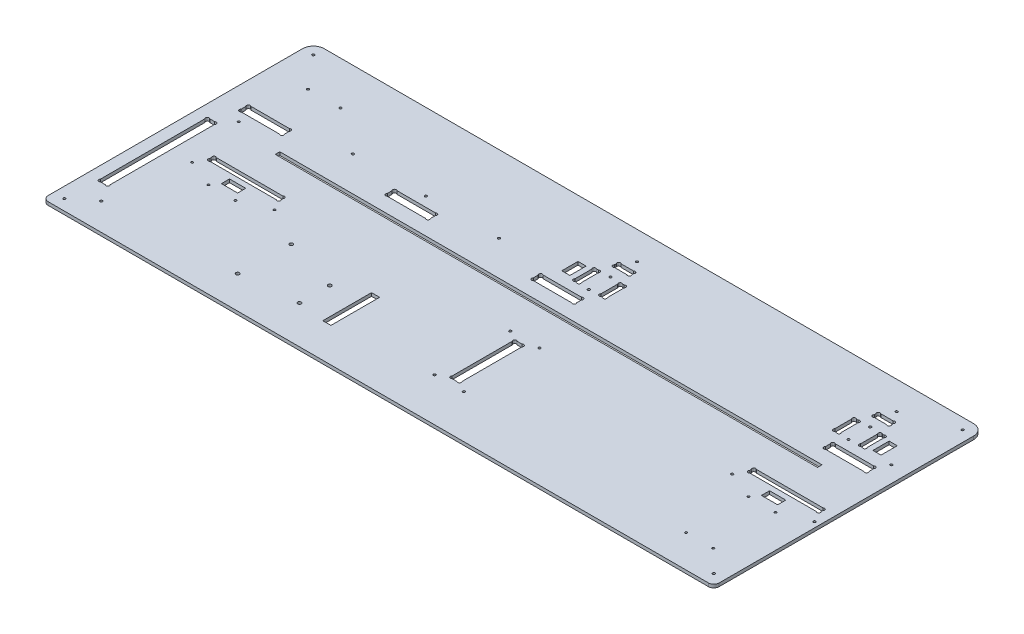
SolidWorks part; units mm, degrees
ref_plane "Plan de face" through (0, 0, 0) normal (0, 0, 1) x (1, 0, 0)
ref_plane "Plan de dessus" through (0, 0, 0) normal (0, 1, 0) x (1, 0, 0)
ref_plane "Plan de droite" through (0, 0, 0) normal (1, 0, 0) x (0, 0, -1)
sketch "Esquisse1" plane through (0, 0, 0) normal (0, 1, 0) x (1, 0, 0)
  line L26 (317, 211.2627) -> (317, 212.7373)
  line L28 (319.2627, 215) -> (330.7373, 215)
  line L29 (333, 211.2627) -> (333, 212.7373)
  line L30 (330.7373, 209) -> (319.2627, 209)
  line L31 (312.2627, 179.5) -> (313.7373, 179.5)
  line L32 (312.2627, 199.5) -> (313.7373, 199.5)
  line L33 (310, 197.2373) -> (310, 181.7627)
  line L34 (316, 181.7627) -> (316, 197.2373)
  line L35 (334, 181.7627) -> (334, 197.2373)
  line L36 (340, 197.2373) -> (340, 181.7627)
  line L37 (337.7373, 199.5) -> (336.2627, 199.5)
  line L38 (337.7373, 179.5) -> (336.2627, 179.5)
  line L39 (552.2627, 179.5) -> (553.7373, 179.5)
  line L40 (552.2627, 199.5) -> (553.7373, 199.5)
  line L41 (550, 197.2373) -> (550, 181.7627)
  line L42 (556, 181.7627) -> (556, 197.2373)
  line L43 (574, 181.7627) -> (574, 197.2373)
  line L44 (580, 197.2373) -> (580, 181.7627)
  line L45 (577.7373, 199.5) -> (576.2627, 199.5)
  line L46 (577.7373, 179.5) -> (576.2627, 179.5)
  line L47 (559.2627, 209) -> (570.7373, 209)
  line L48 (557, 211.2627) -> (557, 212.7373)
  line L49 (570.7373, 215) -> (559.2627, 215)
  line L50 (573, 211.2627) -> (573, 212.7373)
  line L55 (560, 167.7373) -> (560, 163.2627)
  line L56 (600, 167.7373) -> (600, 163.2627)
  line L57 (562.2627, 170) -> (597.7373, 170)
  line L58 (597.7373, 161) -> (562.2627, 161)
  line L59 (292.2627, 161) -> (327.7373, 161)
  line L60 (327.7373, 170) -> (292.2627, 170)
  line L61 (290, 167.7373) -> (290, 163.2627)
  line L62 (330, 167.7373) -> (330, 163.2627)
  line L64 (20, 167.7373) -> (20, 163.2627)
  line L65 (60, 167.7373) -> (60, 163.2627)
  line L66 (22.2627, 170) -> (57.7373, 170)
  line L67 (57.7373, 161) -> (22.2627, 161)
  line L70 (155, 167.7373) -> (155, 163.2627)
  line L71 (195, 167.7373) -> (195, 163.2627)
  line L72 (157.2627, 170) -> (192.7373, 170)
  line L73 (192.7373, 161) -> (157.2627, 161)
  line L76 (10, 250) -> (610, 250)
  line L77 (0, 240) -> (0, 0)
  line L78 (0, 0) -> (620, 0)
  line L79 (620, 240) -> (620, 0)
  line L84 (13.2627, 40) -> (17.7373, 40)
  line L85 (13.2627, 141) -> (17.7373, 141)
  line L86 (11, 138.7373) -> (11, 42.2627)
  line L87 (20, 42.2627) -> (20, 138.7373)
  line L98 (337.7373, 45) -> (333.2627, 45)
  line L99 (337.7373, 105) -> (333.2627, 105)
  line L100 (340, 47.2627) -> (340, 102.7373)
  line L101 (331, 102.7373) -> (331, 47.2627)
  line L109 (610, 109.2627) -> (610, 110.7373)
  line L110 (544, 109.2627) -> (544, 110.7373)
  line L111 (607.7373, 107) -> (546.2627, 107)
  line L112 (546.2627, 113) -> (607.7373, 113)
  line L113 (108.7373, 113) -> (47.2627, 113)
  line L114 (47.2627, 107) -> (108.7373, 107)
  line L115 (111, 109.2627) -> (111, 110.7373)
  line L116 (45, 109.2627) -> (45, 110.7373)
  arc A0 (319.2627, 215) -> (317, 212.7373) centre (318.1314, 213.8686) ccw
  arc A1 (319.2627, 209) -> (317, 211.2627) centre (318.1314, 210.1314) cw
  arc A2 (330.7373, 209) -> (333, 211.2627) centre (331.8686, 210.1314) ccw
  arc A3 (330.7373, 215) -> (333, 212.7373) centre (331.8686, 213.8686) cw
  arc A4 (313.7373, 179.5) -> (316, 181.7627) centre (314.8686, 180.6314) ccw
  arc A5 (312.2627, 179.5) -> (310, 181.7627) centre (311.1314, 180.6314) cw
  arc A6 (312.2627, 199.5) -> (310, 197.2373) centre (311.1314, 198.3686) ccw
  arc A7 (313.7373, 199.5) -> (316, 197.2373) centre (314.8686, 198.3686) cw
  arc A8 (336.2627, 179.5) -> (334, 181.7627) centre (335.1314, 180.6314) cw
  arc A9 (336.2627, 199.5) -> (334, 197.2373) centre (335.1314, 198.3686) ccw
  arc A10 (337.7373, 199.5) -> (340, 197.2373) centre (338.8686, 198.3686) cw
  arc A11 (337.7373, 179.5) -> (340, 181.7627) centre (338.8686, 180.6314) ccw
  arc A12 (552.2627, 179.5) -> (550, 181.7627) centre (551.1314, 180.6314) cw
  arc A13 (552.2627, 199.5) -> (550, 197.2373) centre (551.1314, 198.3686) ccw
  arc A14 (553.7373, 199.5) -> (556, 197.2373) centre (554.8686, 198.3686) cw
  arc A15 (553.7373, 179.5) -> (556, 181.7627) centre (554.8686, 180.6314) ccw
  arc A16 (576.2627, 199.5) -> (574, 197.2373) centre (575.1314, 198.3686) ccw
  arc A17 (577.7373, 199.5) -> (580, 197.2373) centre (578.8686, 198.3686) cw
  arc A18 (577.7373, 179.5) -> (580, 181.7627) centre (578.8686, 180.6314) ccw
  arc A19 (576.2627, 179.5) -> (574, 181.7627) centre (575.1314, 180.6314) cw
  arc A20 (559.2627, 215) -> (557, 212.7373) centre (558.1314, 213.8686) ccw
  arc A21 (559.2627, 209) -> (557, 211.2627) centre (558.1314, 210.1314) cw
  arc A22 (570.7373, 209) -> (573, 211.2627) centre (571.8686, 210.1314) ccw
  arc A23 (570.7373, 215) -> (573, 212.7373) centre (571.8686, 213.8686) cw
  arc A29 (560, 163.2627) -> (562.2627, 161) centre (561.1314, 162.1314) ccw
  arc A30 (560, 167.7373) -> (562.2627, 170) centre (561.1314, 168.8686) cw
  arc A31 (600, 167.7373) -> (597.7373, 170) centre (598.8686, 168.8686) ccw
  arc A32 (600, 163.2627) -> (597.7373, 161) centre (598.8686, 162.1314) cw
  arc A34 (290, 163.2627) -> (292.2627, 161) centre (291.1314, 162.1314) ccw
  arc A35 (290, 167.7373) -> (292.2627, 170) centre (291.1314, 168.8686) cw
  arc A36 (330, 167.7373) -> (327.7373, 170) centre (328.8686, 168.8686) ccw
  arc A37 (330, 163.2627) -> (327.7373, 161) centre (328.8686, 162.1314) cw
  arc A40 (20, 163.2627) -> (22.2627, 161) centre (21.1314, 162.1314) ccw
  arc A41 (20, 167.7373) -> (22.2627, 170) centre (21.1314, 168.8686) cw
  arc A42 (60, 167.7373) -> (57.7373, 170) centre (58.8686, 168.8686) ccw
  arc A43 (60, 163.2627) -> (57.7373, 161) centre (58.8686, 162.1314) cw
  arc A44 (155, 163.2627) -> (157.2627, 161) centre (156.1314, 162.1314) ccw
  arc A45 (155, 167.7373) -> (157.2627, 170) centre (156.1314, 168.8686) cw
  arc A46 (195, 163.2627) -> (192.7373, 161) centre (193.8686, 162.1314) cw
  arc A47 (195, 167.7373) -> (192.7373, 170) centre (193.8686, 168.8686) ccw
  arc A50 (17.7373, 40) -> (20, 42.2627) centre (18.8686, 41.1314) ccw
  arc A52 (13.2627, 40) -> (11, 42.2627) centre (12.1314, 41.1314) cw
  arc A53 (17.7373, 141) -> (20, 138.7373) centre (18.8686, 139.8686) cw
  arc A54 (13.2627, 141) -> (11, 138.7373) centre (12.1314, 139.8686) ccw
  arc A56 (10, 250) -> (0, 240) centre (10, 240) ccw
  arc A57 (610, 250) -> (620, 240) centre (610, 240) cw
  arc A59 (331, 47.2627) -> (333.2627, 45) centre (332.1314, 46.1314) ccw
  arc A60 (340, 47.2627) -> (337.7373, 45) centre (338.8686, 46.1314) cw
  arc A61 (331, 102.7373) -> (333.2627, 105) centre (332.1314, 103.8686) cw
  arc A62 (340, 102.7373) -> (337.7373, 105) centre (338.8686, 103.8686) ccw
  arc A64 (607.7373, 107) -> (610, 109.2627) centre (608.8686, 108.1314) ccw
  circle A65 centre (539, 98) radius 1.1
  arc A66 (607.7373, 113) -> (610, 110.7373) centre (608.8686, 111.8686) cw
  circle A67 centre (615, 98) radius 1.1
  arc A68 (546.2627, 113) -> (544, 110.7373) centre (545.1314, 111.8686) ccw
  arc A69 (546.2627, 107) -> (544, 109.2627) centre (545.1314, 108.1314) cw
  arc A70 (108.7373, 107) -> (111, 109.2627) centre (109.8686, 108.1314) ccw
  arc A71 (108.7373, 113) -> (111, 110.7373) centre (109.8686, 111.8686) cw
  arc A73 (47.2627, 113) -> (45, 110.7373) centre (46.1314, 111.8686) ccw
  arc A75 (47.2627, 107) -> (45, 109.2627) centre (46.1314, 108.1314) cw
  point P1 (337, 199.5)
  point P7 (340, 189.5)
  dimension "D25" = 6
  dimension "D28" = 16
  dimension "D29" = 20
  dimension "D32" = 9.5
  dimension "D33" = 35
  dimension "D39" = 10
  dimension "D49" = 1.1314
  dimension "D57" = 6
  dimension "D55" = 10
  dimension "D62" = 5
  dimension "D63" = 1.6
  dimension "D64" = 9
  dimension "D65" = 1.1314
  dimension "D66" = 1.1314
  dimension "D67" = 620
  dimension "D9" = 2.2627
  dimension "D10" = 1.6
  dimension "D78" = 3.7373
  dimension "D14" = 1.6
  dimension "D36" = 1.6
  dimension "D61" = 1.6
  dimension "D95" = 1.6
  dimension "D107" = 1.6
  dimension "D118" = 1.6
  dimension "D119" = 1.6
  dimension "D128" = 6
  dimension "D141" = 1.6
  dimension "D58" = 2.2
  dimension "D2" = 250
  dimension "D8" = 20
  dimension "D13" = 40
  dimension "D16" = 1.1314
  dimension "D17" = 1.1314
  dimension "D19" = 2.2627
  dimension "D20" = 2.2627
  dimension "D21" = 80
  dimension "D22" = 9
  dimension "D23" = 1.1314
  dimension "D24" = 1.1314
  dimension "D26" = 6
  dimension "D27" = 6
  dimension "D30" = 40
  dimension "D31" = 18
  dimension "D37" = 1.1314
  dimension "D38" = 2.2627
  dimension "D40" = 1.1314
  dimension "D41" = 1.1314
  dimension "D42" = 1.1314
  dimension "D43" = 1.1314
  dimension "D45" = 1
  dimension "D46" = 1.1314
  dimension "D47" = 1.1314
  dimension "D48" = 1.1314
  dimension "D51" = 3.7373
  dimension "D52" = 66
  dimension "D53" = 10
  dimension "D54" = 66
  dimension "D56" = 107
  dimension "D59" = 1.1314
  dimension "D60" = 2.2627
  dimension "D68" = 60
  dimension "D70" = 6
  dimension "D72" = 1.1314
  dimension "D73" = 1.1314
  dimension "D74" = 63.7373
  dimension "D75" = 2.2627
  dimension "D76" = 2.2627
  dimension "D77" = 45
  dimension "D79" = 45
  dimension "D83" = 280
  dimension "D84" = 1.1314
  dimension "D85" = 1.1314
  dimension "D86" = 1.1314
  dimension "D87" = 1.1314
  dimension "D88" = 9
  dimension "D89" = 101
  dimension "D90" = 40
  dimension "D91" = 11
  dimension "D96" = 1.1314
  dimension "D97" = 1.1314
  dimension "D98" = 1.1314
  dimension "D100" = 1.1314
  dimension "D105" = 9
  dimension "D106" = 40
  dimension "D108" = 20
  dimension "D109" = 80
  dimension "D110" = 1.1314
  dimension "D111" = 1.1314
  dimension "D112" = 1.1314
  dimension "D113" = 1.1314
  dimension "D114" = 40
  dimension "D115" = 95
  dimension "D116" = 95
  dimension "D117" = 40
  dimension "D120" = 1.1314
  dimension "D121" = 1.1314
  dimension "D122" = 1.1314
  dimension "D123" = 1.1314
  dimension "D124" = 1.1314
  dimension "D125" = 1.1314
  dimension "D126" = 1.1314
  dimension "D127" = 1.1314
  dimension "D129" = 6
  dimension "D130" = 6
  dimension "D132" = 20
  dimension "D133" = 16
  dimension "D135" = 35
  dimension "D136" = 9.5
  dimension "D139" = 1
  dimension "D140" = 18
  dimension "D142" = 1.1314
  dimension "D143" = 1.1314
  dimension "D144" = 1.1314
  dimension "D145" = 1.1314
  dimension "D146" = 1.1314
  dimension "D147" = 1.1314
  dimension "D148" = 1.1314
  dimension "D149" = 1.1314
  dimension "D150" = 1.1314
  dimension "D151" = 1.1314
  dimension "D152" = 1.1314
  dimension "D153" = 1.1314
  dimension "D154" = 9
  dimension "D155" = 5
extrude "Extrusion1" add sketch "Esquisse1" along normal blind 3
sketch "Esquisse2" plane through (0, 3, 0) normal (0, 1, 0) x (-1, 0, 0)
  line L0 (-610, -250) -> (-10, -250) construction
  line L5 (-620, 21.4973) -> (-620, -261.3021) construction
  line L7 (-573, -142.8) -> (-72, -142.8)
  line L8 (-573, -142.8) -> (-573, -147)
  line L9 (-573, -147) -> (-72, -147)
  line L10 (-72, -142.8) -> (-72, -147)
  dimension "D1" = 47
  dimension "D2" = 4.2
  dimension "D3" = 501
  dimension "D4" = 103
extrude "Enlèv. mat.-Extru.1" cut sketch "Esquisse2" against normal through all
sketch "Esquisse3" plane through (0, 3, 0) normal (0, 1, 0) x (1, 0, 0)
  line L0 (574, 197.2373) -> (574, 181.7627) construction
  line L1 (556, 181.7627) -> (556, 197.2373) construction
  line L2 (559.2627, 209) -> (570.7373, 209) construction
  line L4 (576.2627, 179.5) -> (577.7373, 179.5) construction
  line L5 (577.7373, 199.5) -> (576.2627, 199.5) construction
  line L6 (334, 197.2373) -> (334, 181.7627) construction
  circle A0 centre (565, 179.5) radius 1.1
  circle A1 centre (565, 199.5) radius 1.1
  circle A2 centre (325, 179.5) radius 1.1
  circle A3 centre (325, 199.5) radius 1.1
  dimension "D1" = 2.2
  dimension "D2" = 9
  dimension "D3" = 9
  dimension "D4" = 20
  dimension "D5" = 9.5
  dimension "D6" = 0
  dimension "D7" = 0
  dimension "D8" = 9
extrude "Enlèv. mat.-Extru.2" cut sketch "Esquisse3" against normal through all
fillet "Congé1" radius 5 2 edges at (620, 1.5, 0) (0, 1.5, 0)
sketch "Esquisse4" plane through (0, 0, 0) normal (0, -1, 0) x (1, 0, 0)
  line L0 (0, -240) -> (0, -5) construction
  line L1 (5, 0) -> (615, 0) construction
  line L2 (610, -250) -> (10, -250) construction
  line L3 (620, -5) -> (620, -240) construction
  circle A0 centre (10, -10) radius 1.1
  circle A1 centre (610, -10) radius 1.1
  circle A2 centre (610, -240) radius 1.1
  circle A3 centre (10, -240) radius 1.1
  dimension "D1" = 2.2
  dimension "D2" = 10
  dimension "D3" = 10
  dimension "D4" = 10
  dimension "D5" = 10
  dimension "D6" = 10
  dimension "D7" = 10
  dimension "D8" = 10
  dimension "D9" = 10
extrude "Enlèv. mat.-Extru.3" cut sketch "Esquisse4" against normal through all
sketch "Esquisse5" plane through (0, 3, 0) normal (0, 1, 0) x (1, 0, 0)
  line L1 (0, 240) -> (0, 5) construction
  line L2 (5, 0) -> (615, 0) construction
  circle A0 centre (151.27, 78.26) radius 1.59
  circle A1 centre (150, 30) radius 1.59
  circle A2 centre (202.07, 63.02) radius 1.59
  circle A3 centre (202.07, 35.08) radius 1.59
  dimension "D1" = 3.18
  dimension "D7" = 30
  dimension "D2" = 48.26
  dimension "D3" = 27.94
  dimension "D4" = 52.07
  dimension "D5" = 5.08
  dimension "D6" = 150
  dimension "D8" = 1.27
extrude "Enlèv. mat.-Extru.4" cut sketch "Esquisse5" against normal through all
sketch "Esquisse6" plane through (0, 3, 0) normal (0, 1, 0) x (1, 0, 0)
  line L0 (544, 110.7373) -> (544, 109.2627) construction
  line L1 (569.5, 102) -> (584.5, 102)
  line L2 (569.5, 102) -> (569.5, 94.5)
  line L3 (569.5, 94.5) -> (584.5, 94.5)
  line L4 (584.5, 102) -> (584.5, 94.5)
  line L5 (610, 109.2627) -> (610, 110.7373) construction
  line L6 (546.2627, 107) -> (607.7373, 107) construction
  line L8 (585, 197) -> (592.5, 197)
  line L9 (585, 197) -> (585, 182)
  line L10 (585, 182) -> (592.5, 182)
  line L11 (592.5, 197) -> (592.5, 182)
  line L12 (305, 197) -> (297.5, 197)
  line L13 (305, 197) -> (305, 182)
  line L14 (305, 182) -> (297.5, 182)
  line L15 (297.5, 197) -> (297.5, 182)
  line L16 (577.7373, 199.5) -> (576.2627, 199.5) construction
  line L17 (576.2627, 179.5) -> (577.7373, 179.5) construction
  line L18 (580, 181.7627) -> (580, 197.2373) construction
  line L19 (310, 197.2373) -> (310, 181.7627) construction
  line L20 (313.7373, 199.5) -> (312.2627, 199.5) construction
  line L21 (45, 110.7373) -> (45, 109.2627) construction
  line L22 (227.07, 76.63) -> (234.57, 76.63)
  line L23 (227.07, 76.63) -> (227.07, 31.63)
  line L24 (227.07, 31.63) -> (234.57, 31.63)
  line L25 (234.57, 76.63) -> (234.57, 31.63)
  line L26 (70.5, 102) -> (85.5, 102)
  line L27 (70.5, 102) -> (70.5, 94.5)
  line L28 (70.5, 94.5) -> (85.5, 94.5)
  line L29 (85.5, 102) -> (85.5, 94.5)
  circle A0 centre (150, 30) radius 1.59 construction
  circle A1 centre (151.27, 78.26) radius 1.59 construction
  circle A2 centre (202.07, 63.02) radius 1.59 construction
  dimension "D1" = 15
  dimension "D2" = 7.5
  dimension "D3" = 25.5
  dimension "D4" = 25.5
  dimension "D5" = 5
  dimension "D6" = 7.5
  dimension "D7" = 15
  dimension "D8" = 15
  dimension "D9" = 7.5
  dimension "D10" = 2.5
  dimension "D11" = 2.5
  dimension "D12" = 5
  dimension "D13" = 5
  dimension "D14" = 2.5
  dimension "D15" = 7.5
  dimension "D16" = 45
  dimension "D17" = 1.63
  dimension "D18" = 1.63
  dimension "D19" = 25
  dimension "D20" = 15
  dimension "D21" = 25.5
extrude "Enlèv. mat.-Extru.5" cut sketch "Esquisse6" against normal through all
sketch "Esquisse7" plane through (0, 3, 0) normal (0, 1, 0) x (1, 0, 0)
  line L0 (70.5, 102) -> (70.5, 94.5) construction
  line L1 (85.5, 94.5) -> (85.5, 102) construction
  line L2 (70.5, 94.5) -> (85.5, 94.5) construction
  line L3 (569.5, 94.5) -> (584.5, 94.5) construction
  line L4 (584.5, 94.5) -> (584.5, 102) construction
  line L5 (569.5, 102) -> (569.5, 94.5) construction
  line L6 (47.2627, 107) -> (108.7373, 107) construction
  line L7 (45, 110.7373) -> (45, 109.2627) construction
  line L8 (111, 109.2627) -> (111, 110.7373) construction
  line L9 (5, 0) -> (615, 0) construction
  circle A0 centre (589.5, 87.5) radius 1
  circle A1 centre (564.5, 87.5) radius 1
  circle A6 centre (65.5, 87.5) radius 1
  circle A7 centre (90.5, 87.5) radius 1
  circle A8 centre (116, 98) radius 1
  circle A9 centre (40, 98) radius 1
  circle A10 centre (564.5, 30) radius 1
  circle A11 centre (589.5, 30) radius 1
  dimension "D1" = 2
  dimension "D8" = 2
  dimension "D2" = 5
  dimension "D3" = 5
  dimension "D4" = 7
  dimension "D5" = 7
  dimension "D6" = 5
  dimension "D7" = 5
  dimension "D9" = 30
  dimension "D10" = 5
  dimension "D11" = 9
  dimension "D12" = 5
extrude "Enlèv. mat.-Extru.6" cut sketch "Esquisse7" against normal through all
sketch "Esquisse8" plane through (0, 3, 0) normal (0, 1, 0) x (1, 0, 0)
  line L0 (5, 0) -> (615, 0) construction
  line L1 (0, 240) -> (0, 5) construction
  line L2 (330.7373, 215) -> (319.2627, 215) construction
  line L3 (570.7373, 215) -> (559.2627, 215) construction
  line L4 (597.7373, 170) -> (562.2627, 170) construction
  line L5 (331, 102.7373) -> (331, 47.2627) construction
  line L6 (340, 47.2627) -> (340, 102.7373) construction
  line L7 (192.7373, 170) -> (157.2627, 170) construction
  line L8 (610, 250) -> (10, 250) construction
  circle A0 centre (29, 25) radius 1.1
  circle A1 centre (29, 152) radius 1.1
  circle A2 centre (107.5, 179) radius 1.1
  circle A3 centre (242.5, 179) radius 1.1
  circle A4 centre (175, 179) radius 1.1
  circle A5 centre (325, 224) radius 1.1
  circle A6 centre (565, 224) radius 1.1
  circle A7 centre (605, 179) radius 1.1
  circle A8 centre (35, 210) radius 1.1
  circle A9 centre (322, 40) radius 1.1
  circle A10 centre (322, 110) radius 1.1
  circle A11 centre (349, 110) radius 1.1
  circle A12 centre (349, 40) radius 1.1
  circle A13 centre (65, 210) radius 1.1
  point P22 (565, 215)
  point P24 (325, 215)
  point P49 (175, 170)
  dimension "D1" = 2.2
  dimension "D4" = 127
  dimension "D5" = 67.5
  dimension "D13" = 9
  dimension "D2" = 25
  dimension "D3" = 29
  dimension "D6" = 35
  dimension "D7" = 9
  dimension "D8" = 67.5
  dimension "D9" = 9
  dimension "D10" = 40
  dimension "D11" = 9
  dimension "D12" = 40
  dimension "D14" = 9
  dimension "D15" = 70
  dimension "D16" = 30
  dimension "D17" = 40
extrude "Enlèv. mat.-Extru.7" cut sketch "Esquisse8" against normal through all
